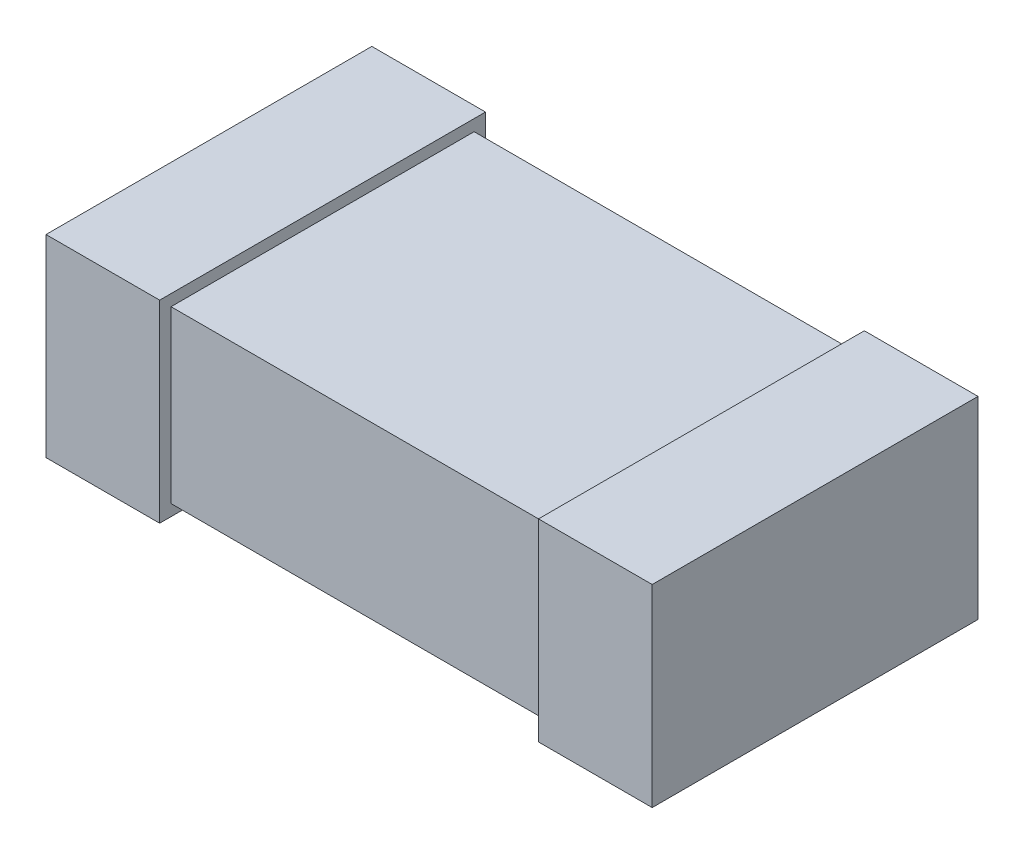
SolidWorks part; units mm, degrees
ref_plane "Front Plane" through (0, 0, 0) normal (0, 0, 1) x (1, 0, 0)
ref_plane "Top Plane" through (0, 0, 0) normal (0, 1, 0) x (1, 0, 0)
ref_plane "Right Plane" through (0, 0, 0) normal (1, 0, 0) x (0, 0, -1)
ref_plane "Plane4" through (0, 0.45, 0) normal (0, 1, 0) x (1, 0, 0)
sketch "Sketch1" plane through (0, 0.45, 0) normal (0, 1, 0) x (1, 0, 0)
  line L0 (-0.5, -0.4) -> (0.5, -0.4)
  line L1 (0.5, -0.4) -> (0.5, 0.4)
  line L2 (0.5, 0.4) -> (-0.5, 0.4)
  line L3 (-0.5, 0.4) -> (-0.5, -0.4)
extrude "Boss-Extrude1" add sketch "Sketch1" against normal blind 0.45
ref_plane "Plane5" through (0, 0, -0.43) normal (0, 0, -1) x (-1, 0, 0)
sketch "Sketch2" plane through (0, 0, -0.43) normal (0, 0, -1) x (-1, 0, 0)
  line L0 (0.8, 0.48) -> (0.5, 0.48)
  line L1 (0.5, 0.48) -> (0.5, -0.03)
  line L2 (0.5, -0.03) -> (0.8, -0.03)
  line L3 (0.8, -0.03) -> (0.8, 0.48)
extrude "Boss-Extrude2" add sketch "Sketch2" against normal blind 0.86
ref_plane "Plane6" through (0.5, 0, 0) normal (-1, 0, 0) x (0, -1, 0)
sketch "Sketch3" plane through (0.5, 0, 0) normal (-1, 0, 0) x (0, -1, 0)
  line L0 (-0.48, 0.43) -> (-0.48, -0.43)
  line L1 (-0.48, -0.43) -> (0.03, -0.43)
  line L2 (0.03, -0.43) -> (0.03, 0.43)
  line L3 (0.03, 0.43) -> (-0.48, 0.43)
extrude "Boss-Extrude3" add sketch "Sketch3" against normal blind 0.3
